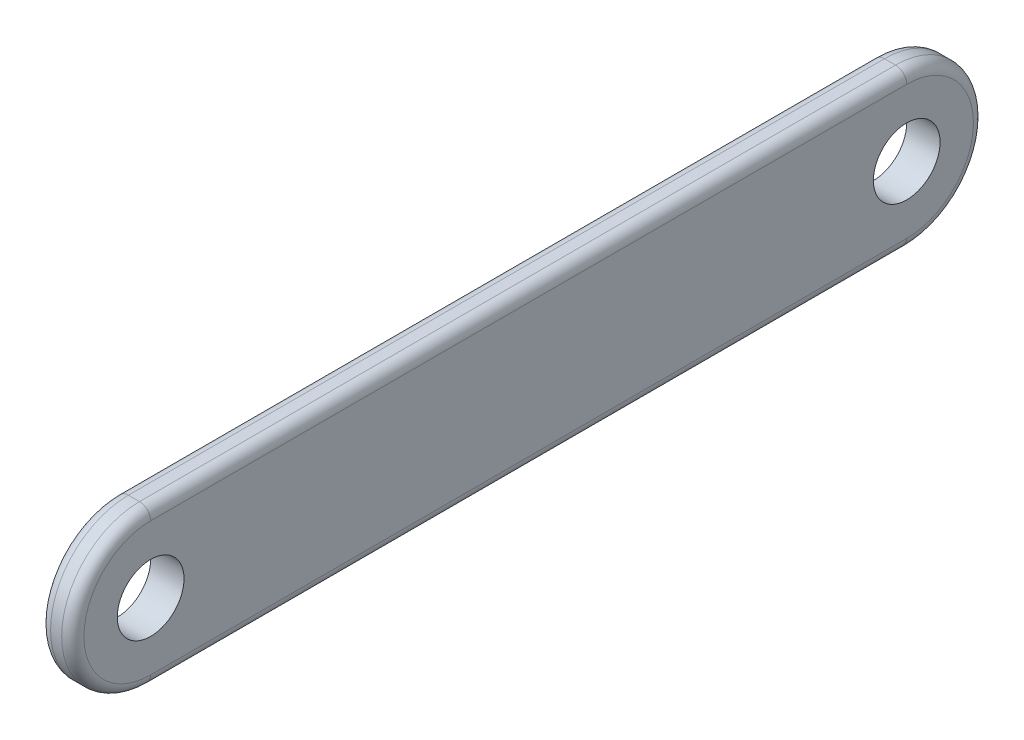
SolidWorks part; units mm, degrees
ref_plane "前视基准面" through (0, 0, 0) normal (0, 0, 1) x (1, 0, 0)
ref_plane "上视基准面" through (0, 0, 0) normal (0, 1, 0) x (1, 0, 0)
ref_plane "右视基准面" through (0, 0, 0) normal (1, 0, 0) x (0, 0, -1)
sketch "草图1" plane through (0, 0, 0) normal (1, 0, 0) x (0, 0, -1)
  line L0 (-34, 0) -> (34, 0) construction
  line L1 (-34, 7) -> (34, 7)
  line L2 (-34, -7) -> (34, -7)
  arc A0 (-34, 7) -> (-34, -7) centre (-34, 0) ccw
  arc A1 (34, -7) -> (34, 7) centre (34, 0) ccw
  circle A2 centre (-34, 0) radius 3
  circle A3 centre (34, 0) radius 3
  point P2 (0, 0)
  dimension "D2" = 7
  dimension "D3" = 6
  dimension "D1" = 68
extrude "凸台-拉伸1" add sketch "草图1" along normal blind 3
fillet "圆角1" radius 1 8 edges at (0, 7, 0) (0, 0, -41) (0, -7, 0) (3, 7, 0) (3, 0, -41) (3, -7, 0) (0, 0, 41) (3, 0, 41)
